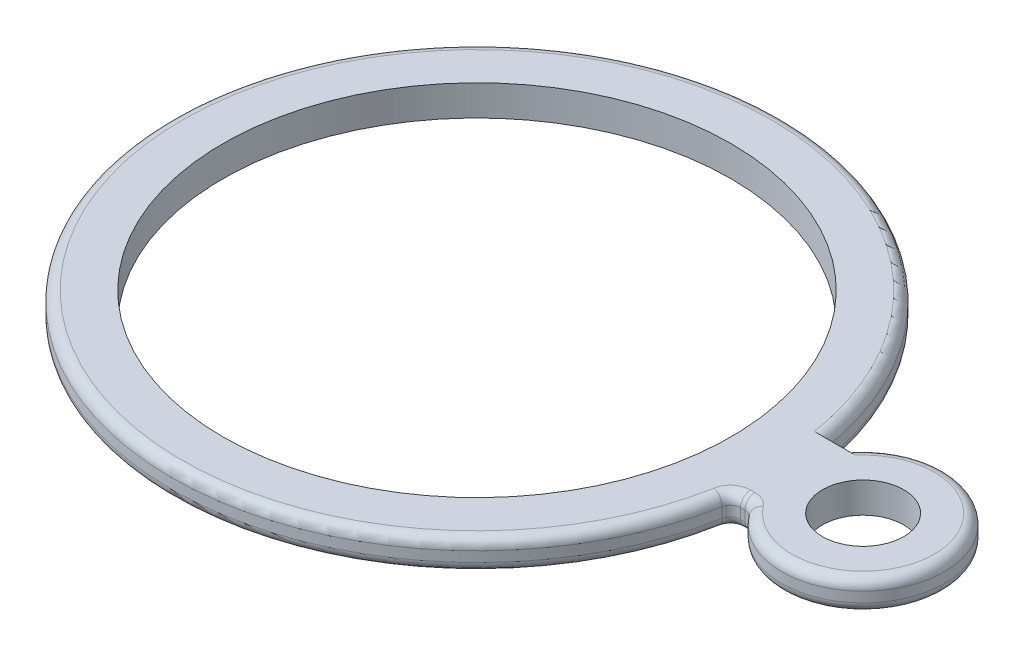
SolidWorks part; units mm, degrees
ref_plane "Front Plane" through (0, 0, 0) normal (0, 0, 1) x (1, 0, 0)
ref_plane "Top Plane" through (0, 0, 0) normal (0, 1, 0) x (1, 0, 0)
ref_plane "Right Plane" through (0, 0, 0) normal (1, 0, 0) x (0, 0, -1)
sketch "Sketch1" plane through (0, 0, 0) normal (0, 1, 0) x (1, 0, 0)
  line L0 (29.6511, 4.5617) -> (31.428, 4.5617)
  line L1 (29.6511, -4.5617) -> (31.428, -4.5617)
  line L2 (0, 0) -> (38, 0)
  circle A0 centre (0, 0) radius 25
  circle A1 centre (0, 0) radius 30
  circle A2 centre (38, 0) radius 4
  circle A3 centre (38, 0) radius 8
  point P10 (0, 0)
  dimension "D1" = 5
  dimension "D2" = 50
  dimension "D3" = 8
extrude "Boss-Extrude1" add sketch "Sketch1" along normal blind 3
fillet "Fillet1" radius 1 8 edges at (-30, 0, 0) (-30, 3, 0) (46, 0, 0) (46, 3, 0) (29.6511, 1.5, 4.5617) (30.5396, 0, 4.5617) (30.5396, 3, 4.5617) (31.428, 1.5, 4.5617)
